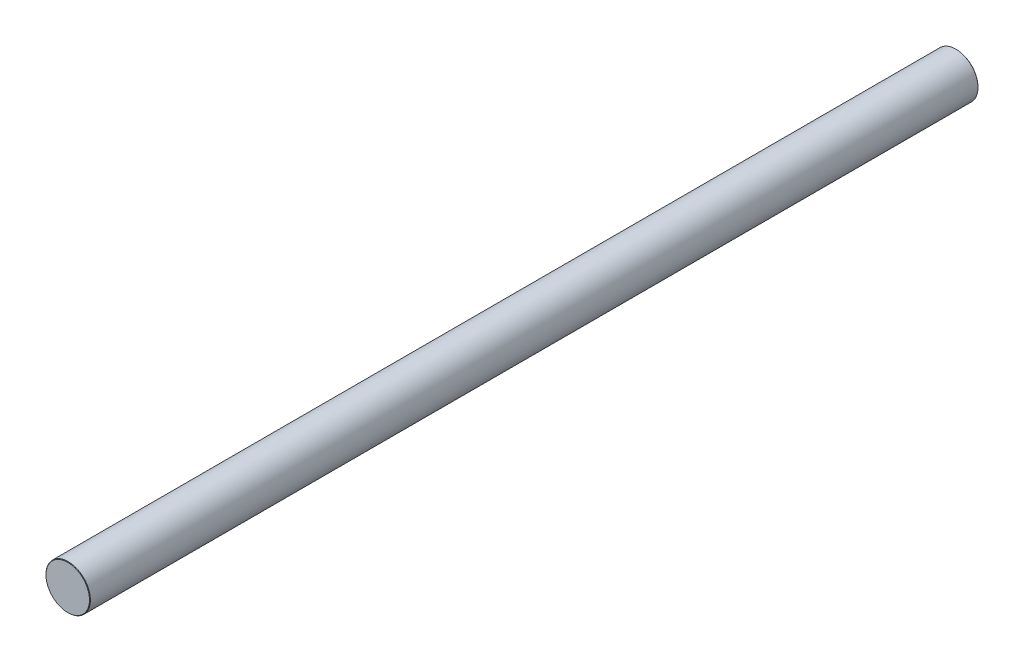
SolidWorks part; units mm, degrees
material "АД 31 ГОСТ 4784-97"
ref_plane "Plane1" through (0, 0, 0) normal (0, 0, 1) x (1, 0, 0)
ref_plane "Plane2" through (0, 0, 0) normal (0, 1, 0) x (1, 0, 0)
ref_plane "Plane3" through (0, 0, 0) normal (1, 0, 0) x (0, 0, -1)
sketch "Эскиз1" plane through (0, 0, 0) normal (0, 0, 1) x (1, 0, 0)
  circle A0 centre (0, 0) radius 5
  dimension "D1" = 10
extrude "Бобышка-Вытянуть1" add sketch "Эскиз1" along normal blind 200
chamfer "Фаска1" distance 0.1 angle 45 2 edges at (5, 0, 0) (5, 0, 200)
